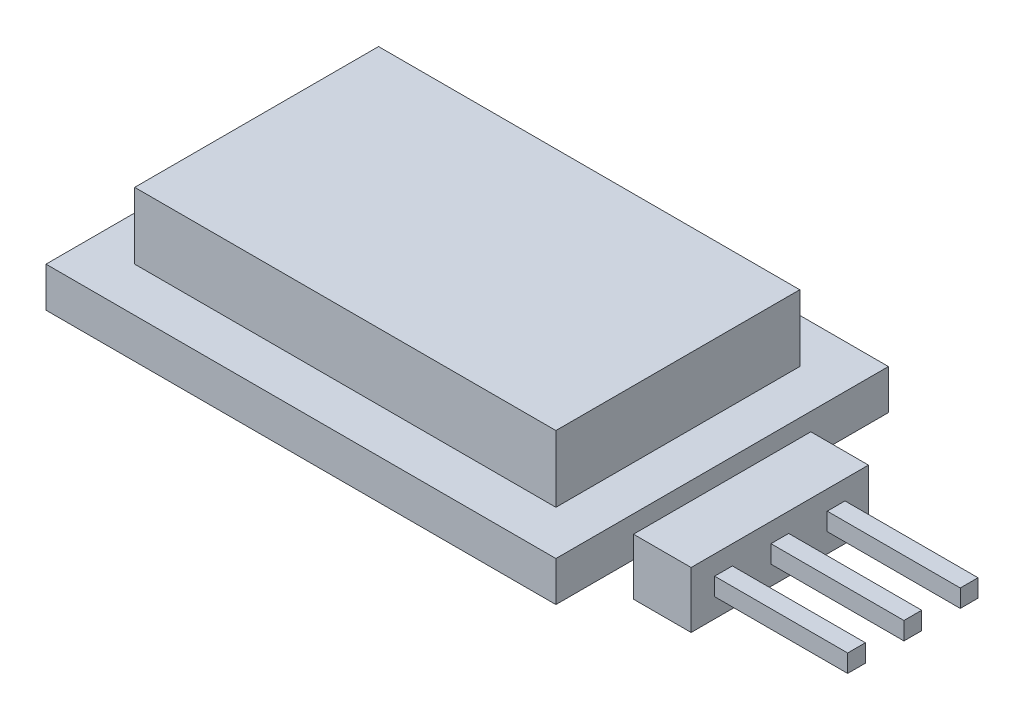
SolidWorks part; units mm, degrees
ref_plane "Alzado" through (0, 0, 0) normal (0, 0, 1) x (1, 0, 0)
ref_plane "Planta" through (0, 0, 0) normal (0, 1, 0) x (1, 0, 0)
ref_plane "Vista lateral" through (0, 0, 0) normal (1, 0, 0) x (0, 0, -1)
sketch "Croquis1" plane through (0, 0, 0) normal (0, 1, 0) x (1, 0, 0)
  line L1 (0, 0) -> (23, 0)
  line L2 (0, 0) -> (0, 15)
  line L3 (0, 15) -> (23, 15)
  line L4 (23, 0) -> (23, 15)
  dimension "D1" = 23
  dimension "D2" = 15
extrude "Saliente-Extruir1" add sketch "Croquis1" along normal blind 1.8
sketch "Croquis2" plane through (0, 1.8, 0) normal (0, 1, 0) x (1, 0, 0)
  line L0 (0, 15) -> (0, 0) construction
  line L1 (2, 2) -> (21, 2)
  line L2 (2, 2) -> (2, 13)
  line L3 (2, 13) -> (21, 13)
  line L4 (21, 2) -> (21, 13)
  line L5 (23, 15) -> (0, 15) construction
  line L6 (0, 0) -> (23, 0) construction
  line L7 (23, 0) -> (23, 15) construction
  dimension "D1" = 2
  dimension "D2" = 2
  dimension "D3" = 2
  dimension "D4" = 2
extrude "Saliente-Extruir2" add sketch "Croquis2" along normal blind 3
sketch "Croquis3" plane through (23, 0, 0) normal (1, 0, 0) x (0, 0, -1)
  line L0 (0, 1.8) -> (15, 1.8) construction
  line L1 (3.5, 1) -> (11.5, 1)
  line L2 (3.5, 1) -> (3.5, -1.54)
  line L3 (3.5, -1.54) -> (11.5, -1.54)
  line L4 (11.5, 1) -> (11.5, -1.54)
  line L5 (2, 1.8) -> (13, 1.8) construction
  point P6 (7.5, 1)
  point P9 (7.5, 1.8)
  dimension "D1" = 2.54
  dimension "D2" = 0.8
  dimension "D3" = 8
extrude "Saliente-Extruir3" add sketch "Croquis3" along normal blind 2.6
sketch "Croquis4" plane through (25.6, 0, 0) normal (1, 0, 0) x (0, 0, -1)
  line L0 (3.5, -1.54) -> (11.5, 1) construction
  line L1 (9.64, 0.13) -> (9.64, -0.67)
  line L2 (7.1, 0.13) -> (7.9, 0.13)
  line L3 (7.1, 0.13) -> (7.1, -0.67)
  line L4 (7.1, -0.67) -> (7.9, -0.67)
  line L5 (7.9, 0.13) -> (7.9, -0.67)
  line L6 (7.1, 0.13) -> (7.9, -0.67) construction
  line L7 (7.1, -0.67) -> (7.9, 0.13) construction
  line L8 (9.64, 0.13) -> (10.44, 0.13)
  line L9 (10.44, 0.13) -> (10.44, -0.67)
  line L10 (9.64, -0.67) -> (10.44, -0.67)
  line L11 (4.56, 0.13) -> (5.36, 0.13)
  line L12 (5.36, 0.13) -> (5.36, -0.67)
  line L13 (4.56, -0.67) -> (5.36, -0.67)
  line L14 (4.56, 0.13) -> (4.56, -0.67)
  point P4 (7.5, -0.27)
  dimension "D1" = 0.8
  dimension "D2" = 0.8
  dimension "D3" = 2
  dimension "D4" = 2
extrude "Saliente-Extruir4" add sketch "Croquis4" along normal blind 6
